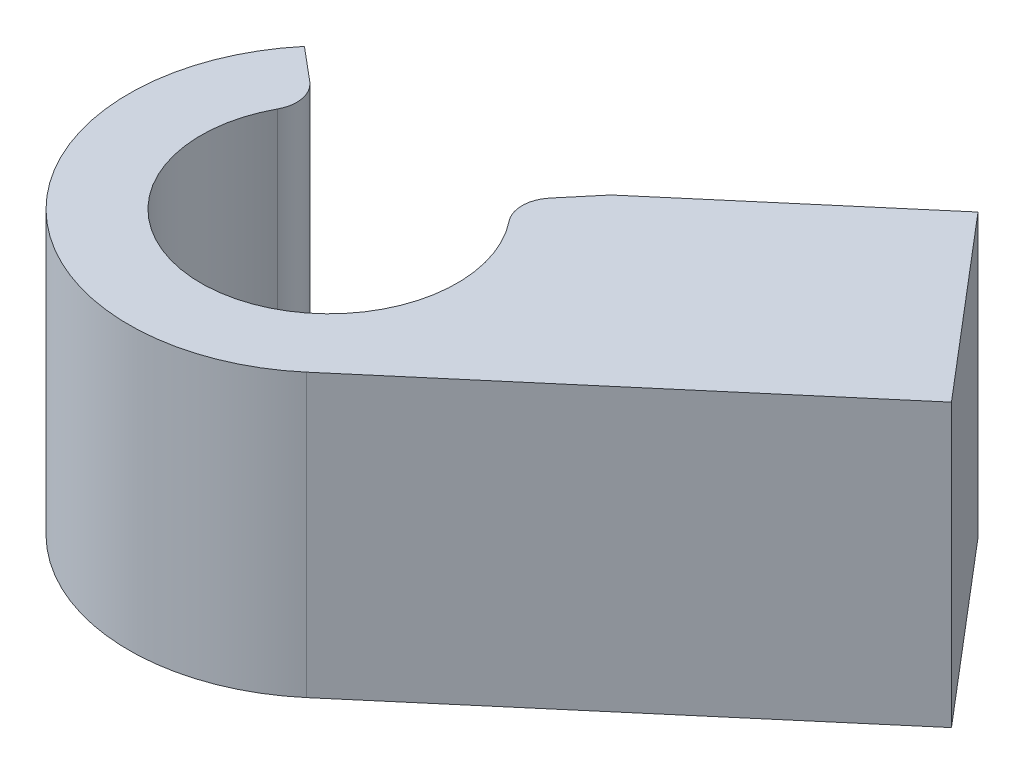
SolidWorks part; units mm, degrees
material "6061-T6 (SS)"
ref_plane "Front Plane" through (0, 0, 0) normal (0, 0, 1) x (1, 0, 0)
ref_plane "Top Plane" through (0, 0, 0) normal (0, 1, 0) x (1, 0, 0)
ref_plane "Right Plane" through (0, 0, 0) normal (1, 0, 0) x (0, 0, -1)
sketch "Sketch1" plane through (0, 0, 0) normal (0, 1, 0) x (1, 0, 0)
  circle A0 centre (0, 0) radius 12.5
  dimension "D2" = 25
extrude "Boss-Extrude1" add sketch "Sketch1" along normal blind 17.6
sketch "Sketch2" plane through (0, 17.6, 0) normal (0, 1, 0) x (1, 0, 0)
  circle A0 centre (0, 0) radius 5.5
  dimension "D1" = 11
extrude "Cut-Extrude1" cut sketch "Sketch2" against normal blind 50.8
sketch "Sketch3" plane through (0, 17.6, 0) normal (0, 1, 0) x (1, 0, 0)
  circle A0 centre (0, 0) radius 8
  dimension "D1" = 16
extrude "Cut-Extrude3" cut sketch "Sketch3" against normal offset from surface (15.6 mm away) 2 up to face at (0, 0, 5.5)
sketch "Sketch4" plane through (0, 17.6, 0) normal (0, 1, 0) x (1, 0, 0)
  line L0 (0, 0) -> (14.4876, 17.2657)
  line L1 (0, 0) -> (-19.972, 16.7585)
  line L2 (0, 0) -> (0, 22.9529) construction
  line L3 (0, 0) -> (-17.2058, 0) construction
  circle A0 centre (0, 0) radius 8 construction
  circle A1 centre (0, 0) radius 12.5 construction
  circle A2 centre (0, 0) radius 8
  circle A3 centre (0, 0) radius 12.5
  circle M3 centre (0, 0) radius 8
  circle M4 centre (0, 0) radius 12.5
  dimension "D1" = 90
  dimension "D2" = 40
extrude "Cut-Extrude4" cut sketch "Sketch4" against normal through all contours L1 L0 M3 M4
sketch "Sketch5" plane through (0, 17.6, 0) normal (0, 1, 0) x (1, 0, 0)
  line L0 (20.4113, 20.1062) -> (8.0348, 9.5756)
  line L1 (8.1004, -9.5202) -> (29.8635, 8.9973)
  line L2 (29.8635, 8.9973) -> (20.4113, 20.1062)
  arc A0 (-9.5756, 8.0348) -> (8.0348, 9.5756) centre (0, 0) ccw construction
  arc A1 (-9.5756, 8.0348) -> (8.0348, 9.5756) centre (0, 0) ccw
  point P0 (0, 0)
  dimension "D1" = 28.575
extrude "Boss-Extrude2" add sketch "Sketch5" against normal through all
fillet "Fillet1" radius 2 2 edges at (-6.1284, 9.8, -5.1423) (5.1423, 9.8, -6.1284)
equation "\"1.1c\"=0.0104601"
